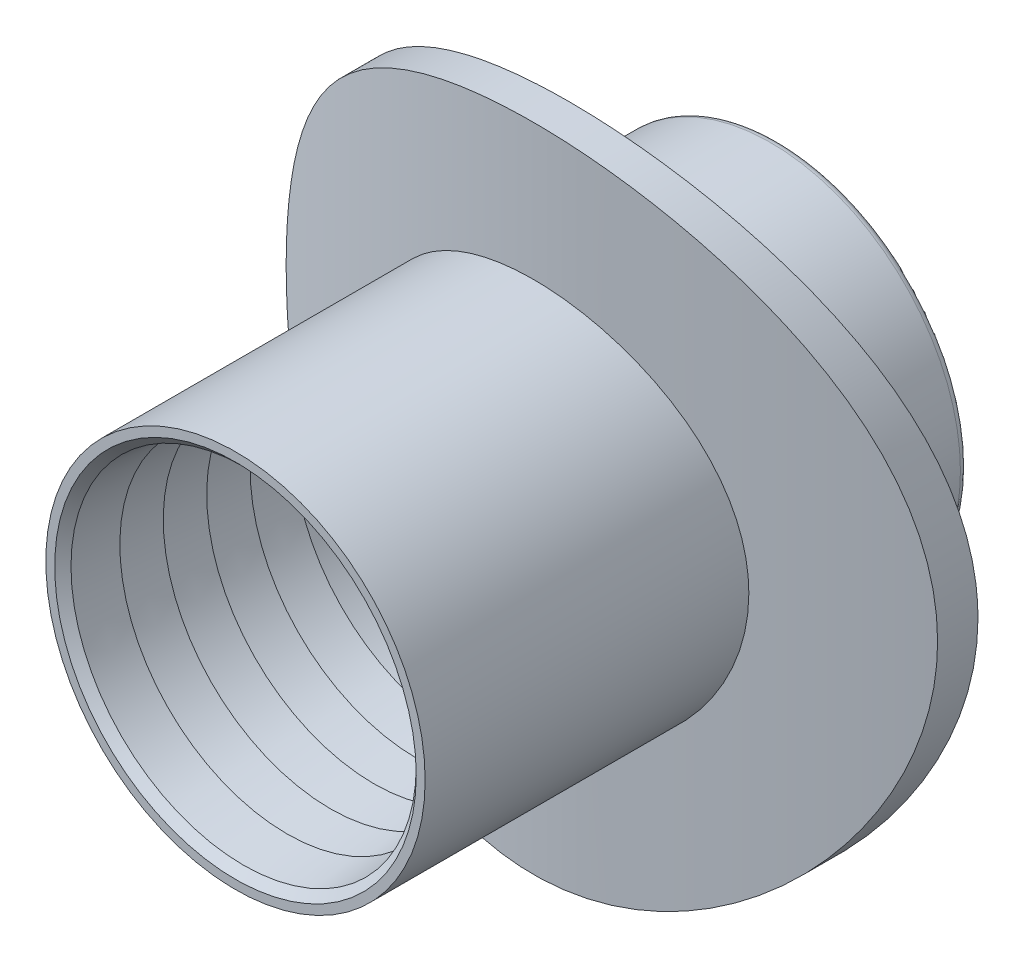
SolidWorks part; units mm, degrees
ref_plane "Front Plane" through (0, 0, 0) normal (0, 0, 1) x (1, 0, 0)
ref_plane "Top Plane" through (0, 0, 0) normal (0, 1, 0) x (1, 0, 0)
ref_plane "Right Plane" through (0, 0, 0) normal (1, 0, 0) x (0, 0, -1)
sketch "Sketch1" plane through (0, 0, 0) normal (0, 1, 0) x (1, 0, 0)
  circle A0 centre (0, 0) radius 62.75
  dimension "D1" = 125.5
ref_plane "Plane1" through (0, 0, 63.5) normal (0, 0, 1) x (1, 0, 0)
sketch "Sketch2" plane through (0, 0, 63.5) normal (0, 0, 1) x (1, 0, 0)
  circle A0 centre (0, 0) radius 30
  dimension "D1" = 60
extrude "Boss-Extrude4" add sketch "Sketch2" along normal blind 2.54 and the other way blind 12.7 contours A0
extrude "Cut-Extrude5" cut sketch "Sketch1" against normal through all and the other way through all contours A0
sketch "Sketch11" plane through (0, 0, 0) normal (0, 1, 0) x (1, 0, 0)
  line L0 (31.285, -58.1595) -> (31.285, -70.9755)
  line L1 (31.285, -70.9755) -> (-30.8594, -70.9755)
  line L2 (-30.8594, -70.9755) -> (-30.8594, -58.3865)
  arc A0 (-30.8594, -58.3865) -> (31.285, -58.1595) centre (0, 0) ccw
  dimension "D1" = 66.04
extrude "Cut-Extrude6" cut sketch "Sketch11" against normal through all and the other way through all
sketch "Sketch12" plane through (0, 0, 63.5) normal (0, 0, 1) x (1, 0, 0)
  circle A0 centre (0, 0) radius 17.47
  dimension "D1" = 34.94
sketch "Sketch18" plane through (0, 0, 0) normal (0, 1, 0) x (1, 0, 0)
  line L0 (0, -61.7757) -> (0, -65.4741)
extrude "Boss-Extrude7" add sketch "Sketch12" along normal blind 30 and the other way blind 20 contours A0
sketch "Sketch20" plane through (0, 0, 93.5) normal (0, 0, 1) x (1, 0, 0)
  circle A0 centre (0, 0) radius 15.9
  dimension "D1" = 31.8
extrude "Cut-Extrude8" cut sketch "Sketch20" against normal through all contours A0
chamfer "Chamfer1" distance 0.75 angle 45 1 edges at (15.9, 0, 93.5)
fillet "Fillet1" radius 0.7 2 edges at (17.47, 0, 43.5) (15.9, 0, 43.5)
sketch "Sketch23" plane through (0, 0, 0) normal (1, 0, 0) x (0, 0, -1)
  line L0 (-92.75, 15.9) -> (-88.75, 15.9)
  line L1 (-44.2, 15.9) -> (-92.75, 15.9) construction
  line L2 (-88.75, 15.9) -> (-88.75, 15.4)
  line L3 (-88.75, 15.4) -> (-92.75, 15.9)
  dimension "D1" = 4
  dimension "D2" = 0.5
sketch "Sketch22" plane through (0, 0, 0) normal (1, 0, 0) x (0, 0, -1)
  line L0 (-93.5, 0) -> (-67.6825, 0)
  line L1 (-93.5, 17.47) -> (-93.5, -17.47) construction
revolve "Revolve1" add sketch "Sketch23" angle 360 about L0
pattern_linear "LPattern1" count 5 spacing 4 along (0, 0, -1) of "Revolve1"
